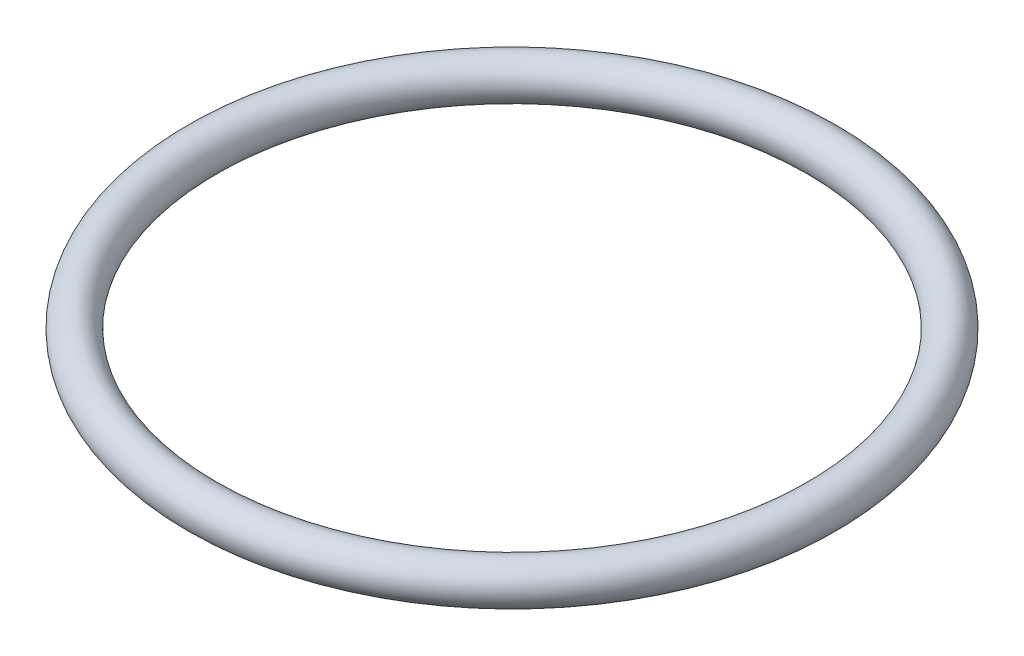
SolidWorks part; units mm, degrees
ref_plane "前视基准面" through (0, 0, 0) normal (0, 0, 1) x (1, 0, 0)
ref_plane "上视基准面" through (0, 0, 0) normal (0, 1, 0) x (1, 0, 0)
ref_plane "右视基准面" through (0, 0, 0) normal (1, 0, 0) x (0, 0, -1)
other "Configuration Table"
sketch "草图1" plane through (0, 0, 0) normal (0, 0, 1) x (1, 0, 0)
  line L0 (0, 0) -> (108, 0) construction
  line L1 (115, 0) -> (115, 29.0176) construction
  line L2 (0, 0) -> (0, 48.7359) construction
  circle A0 centre (108, 0) radius 7
  dimension "D1" = 14
  dimension "D2" = 115
revolve "旋转1" add sketch "草图1" angle 360 about L2
